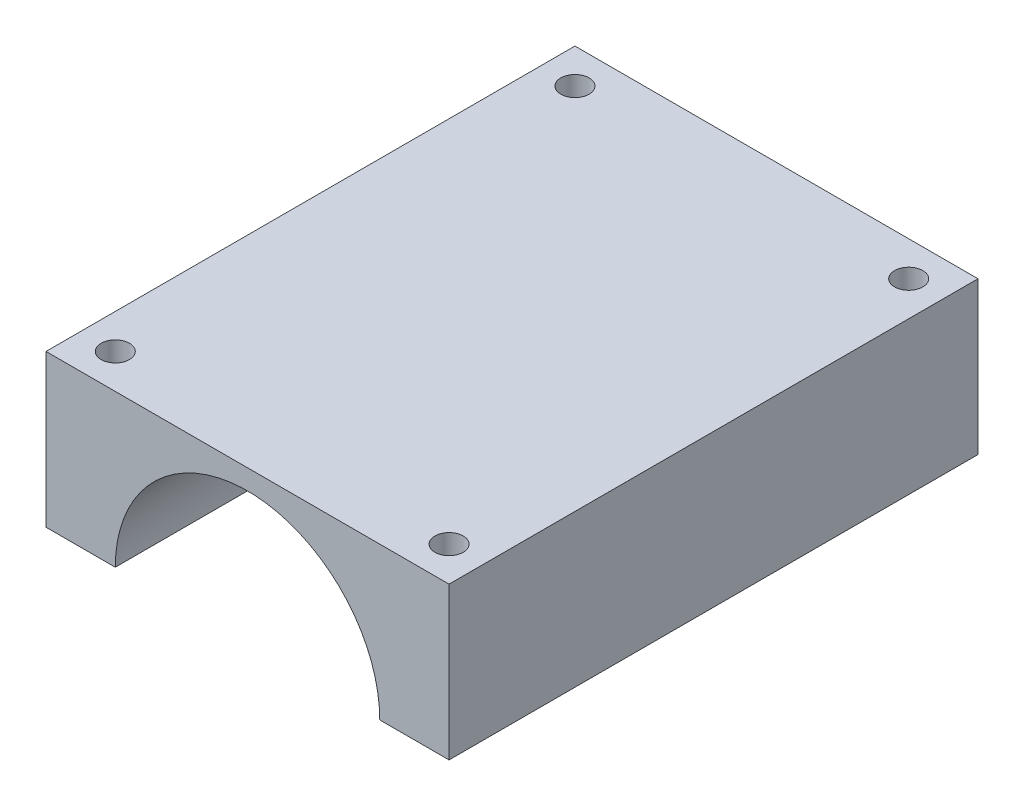
SolidWorks part; units mm, degrees
ref_plane "Front Plane" through (0, 0, 0) normal (0, 0, 1) x (1, 0, 0)
ref_plane "Top Plane" through (0, 0, 0) normal (0, 1, 0) x (1, 0, 0)
ref_plane "Right Plane" through (0, 0, 0) normal (1, 0, 0) x (0, 0, -1)
sketch "Sketch1" plane through (0, 0, 0) normal (0, 1, 0) x (1, 0, 0)
  line L1 (-28.575, 37.5) -> (28.575, 37.5)
  line L2 (-28.575, 37.5) -> (-28.575, -37.5)
  line L3 (-28.575, -37.5) -> (28.575, -37.5)
  line L4 (28.575, 37.5) -> (28.575, -37.5)
  point P4 (0, 37.5)
  point P6 (-28.575, 0)
  dimension "D1" = 57.15
  dimension "D2" = 75
extrude "Boss-Extrude1" add sketch "Sketch1" along normal blind 21.59
sketch "Sketch3" plane through (0, 0, 37.5) normal (0, 0, 1) x (1, 0, 0)
  line L0 (-18.75, 0) -> (18.75, 0)
  line L1 (-28.575, 0) -> (28.575, 0) construction
  arc A0 (-18.75, 0) -> (18.75, 0) centre (0, 0) cw
  point P5 (0, 0)
  dimension "D1" = 37.5
extrude "Cut-Extrude1" cut sketch "Sketch3" against normal up to next
sketch "Sketch5" plane through (0, 21.59, 0) normal (0, 1, 0) x (1, 0, 0)
  line L0 (-18.75, -37.5) -> (-18.75, 37.5) construction
  line L1 (-28.575, 37.5) -> (-28.575, -37.5) construction
  line L2 (-18.75, -37.5) -> (-28.575, -37.5)
  line L3 (-18.75, -37.5) -> (-18.75, -27.675)
  line L4 (-18.75, -27.675) -> (-28.575, -27.675)
  line L5 (-28.575, -37.5) -> (-28.575, -27.675)
  line L6 (-28.575, -37.5) -> (-18.75, -27.675) construction
  circle A0 centre (-23.6625, -32.5875) radius 2.008
  dimension "D1" = 4.016
extrude "Cut-Extrude5" cut sketch "Sketch5" against normal up to next (21.59 mm away) contours A0
mirror "Mirror1" about plane through (0, 0, 0) normal (1, 0, 0) of "Cut-Extrude5" second plane through (0, 0, 0) second plane normal (0, 0, 1)
